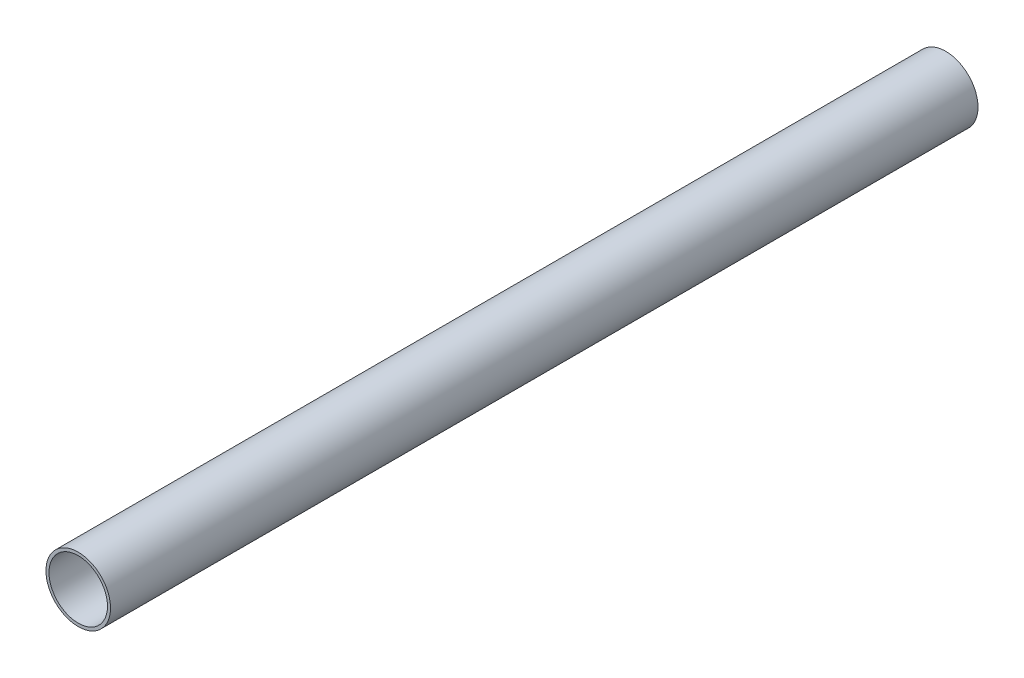
SolidWorks part; units mm, degrees
ref_plane "前视基准面" through (0, 0, 0) normal (0, 0, 1) x (1, 0, 0)
ref_plane "上视基准面" through (0, 0, 0) normal (0, 1, 0) x (1, 0, 0)
ref_plane "右视基准面" through (0, 0, 0) normal (1, 0, 0) x (0, 0, -1)
sketch "草图1" plane through (0, 0, 0) normal (0, 0, 1) x (1, 0, 0)
  circle A0 centre (0, 0) radius 16
  circle A1 centre (0, 0) radius 14.5
  dimension "D1" = 32
  dimension "D2" = 1.5
extrude "凸台-拉伸1" add sketch "草图1" along normal mid plane 430
